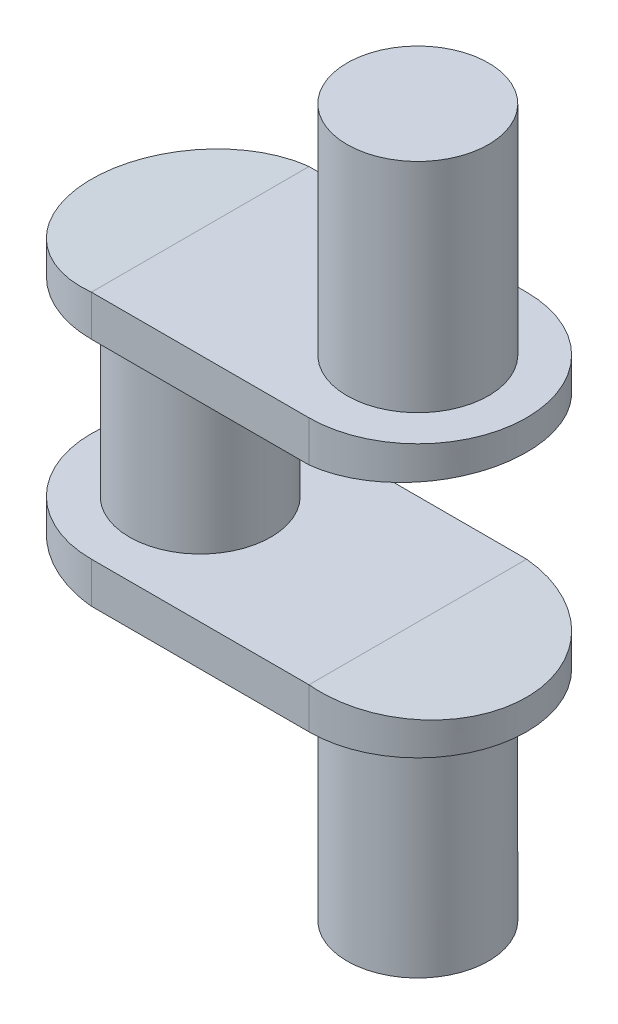
SolidWorks part; units mm, degrees
ref_plane "Front Plane" through (0, 0, 0) normal (0, 0, 1) x (1, 0, 0)
ref_plane "Top Plane" through (0, 0, 0) normal (0, 1, 0) x (1, 0, 0)
ref_plane "Right Plane" through (0, 0, 0) normal (1, 0, 0) x (0, 0, -1)
sketch "Sketch1" plane through (0, 0, 0) normal (0, 1, 0) x (1, 0, 0)
  circle A0 centre (0, 0) radius 26
  dimension "D1" = 52
extrude "Boss-Extrude1" add sketch "Sketch1" along normal mid plane 70
sketch "Sketch2" plane through (0, -35, 0) normal (0, -1, 0) x (1, 0, 0)
  line L0 (0, 40) -> (80, 40)
  line L1 (0, -40) -> (80, -40)
  arc A0 (0, 40) -> (0, -40) centre (0, 0) ccw
  arc A1 (80, 40) -> (80, -40) centre (80, 0) cw
  dimension "D1" = 40
  dimension "D4" = 40
  dimension "D2" = 80
  dimension "D3" = 80
extrude "Boss-Extrude2" add sketch "Sketch2" along normal blind 15
mirror "Mirror1" about plane through (0, 0, 0) normal (0, 1, 0) of "Boss-Extrude2"
sketch "Sketch3" plane through (0, 50, 0) normal (0, 1, 0) x (1, 0, 0)
  circle A0 centre (80, 0) radius 26
  dimension "D1" = 52
extrude "Boss-Extrude3" add sketch "Sketch3" along normal blind 80
mirror "Mirror2" about plane through (0, 0, 0) normal (0, 1, 0) of "Boss-Extrude3"
sketch "Sketch4" plane through (0, 0, 0) normal (0, 0, 1) x (1, 0, 0)
  line L0 (0, 0) -> (292.1389, 0) construction
  line L1 (0, -50) -> (-40, -50)
  line L2 (-40, -50) -> (-40, -46)
  line L3 (-40, -46) -> (0, -50)
  line L4 (80, -35) -> (120, -35)
  line L5 (120, -35) -> (80, -35) construction
  line L6 (120, -35) -> (120, -39)
  line L7 (120, -50) -> (120, -35) construction
  line L8 (120, -39) -> (80, -35)
  line L9 (120, 39) -> (80, 35)
  line L10 (120, 35) -> (120, 39)
  line L11 (80, 35) -> (120, 35)
  line L12 (-40, 46) -> (0, 50)
  line L13 (-40, 50) -> (-40, 46)
  line L14 (0, 50) -> (-40, 50)
  dimension "D1" = 4
  dimension "D2" = 4
extrude "Cut-Extrude1" cut sketch "Sketch4" against normal through all both and the other way through all
